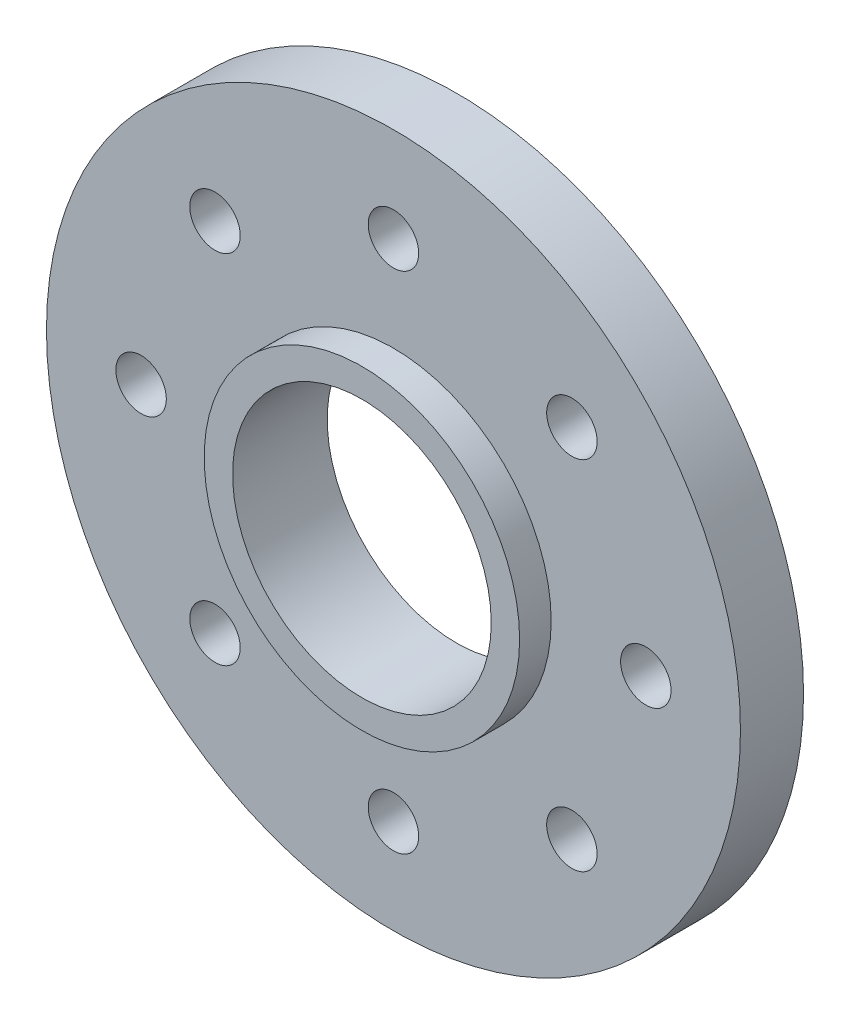
SolidWorks part; units mm, degrees
material "2024 Alloy (SN)"
ref_plane "Front Plane" through (0, 0, 0) normal (0, 0, 1) x (1, 0, 0)
ref_plane "Top Plane" through (0, 0, 0) normal (0, 1, 0) x (1, 0, 0)
ref_plane "Right Plane" through (0, 0, 0) normal (1, 0, 0) x (0, 0, -1)
sketch "Sketch1" plane through (0, 0, 0) normal (0, 0, 1) x (1, 0, 0)
  circle A0 centre (0, 0) radius 4.1
  circle A1 centre (0, 0) radius 11
  dimension "D1" = 8.2
  dimension "D2" = 22
extrude "Boss-Extrude1" add sketch "Sketch1" along normal blind 2
sketch "Sketch2" plane through (0, 0, 2) normal (0, 0, 1) x (1, 0, 0)
  circle A0 centre (0, 0) radius 8
  circle A1 centre (0, 8) radius 1.2841
  circle A2 centre (5.6569, 5.6569) radius 1.2841
  circle A3 centre (8, 0) radius 1.2841
  circle A4 centre (5.6569, -5.6569) radius 1.2841
  circle A5 centre (0, -8) radius 1.2841
  circle A6 centre (-5.6569, -5.6569) radius 1.2841
  circle A7 centre (-8, 0) radius 1.2841
  circle A8 centre (-5.6569, 5.6569) radius 1.2841
  dimension "D1" = 16
  dimension "D2" = 8
hole_wizard "M2x0.4 Tapped Hole1" positions "Sketch4" profile "Sketch3" tap size "M2x0.4" standard "Ansi Metric"
sketch "Sketch4" plane through (0, 0, 2) normal (0, 0, 1) x (1, 0, 0)
  point P0 (0, 8)
  point P1 (5.6569, 5.6569)
  point P4 (8, 0)
  point P7 (5.6569, -5.6569)
  point P10 (0, -8)
  point P13 (-5.6569, -5.6569)
  point P16 (-8, 0)
  point P19 (-5.6569, 5.6569)
sketch "Sketch3" plane through (0, 8, 2) normal (1, 0, 0) x (0, -1, 0)
  line L0 (0, 0) -> (0, 5.6807)
  line L1 (0, 5.6807) -> (0.8, 5.2)
  line L2 (0.8, 5.2) -> (0.8, 0)
  line L5 (0.8, 0) -> (0, 0)
  line L10 (0, 5.6807) -> (-0.8, 5.2) construction
  line L11 (0, -6.35) -> (0, 107.95) construction
  dimension "Tap Drill Dia." = 1.6
  dimension "Tap Drill Depth" = 5.2
  dimension "Drill Angle" = 118
cosmetic thread "Hole Thread1" parameters "D1"=2, "D2"=2
cosmetic thread "Hole Thread2" parameters "D1"=2, "D2"=2
cosmetic thread "Hole Thread3" parameters "D1"=2, "D2"=2
cosmetic thread "Hole Thread4" parameters "D1"=2, "D2"=2
cosmetic thread "Hole Thread5" parameters "D1"=2, "D2"=2
cosmetic thread "Hole Thread6" parameters "D1"=2, "D2"=2
cosmetic thread "Hole Thread7" parameters "D1"=2, "D2"=2
cosmetic thread "Hole Thread8" parameters "D1"=2, "D2"=2
sketch "Sketch5" plane through (0, 0, 2) normal (0, 0, 1) x (1, 0, 0)
  circle A0 centre (0, 0) radius 4.1
  circle A1 centre (0, 0) radius 5
  dimension "D1" = 10
  dimension "D2" = 8.2
extrude "Boss-Extrude2" add sketch "Sketch5" along normal blind 1
